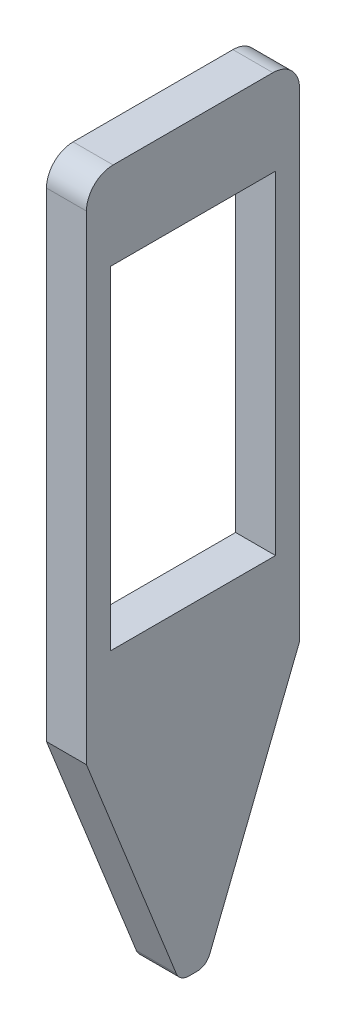
SolidWorks part; units mm, degrees
material "Teca"
ref_plane "Front Plane" through (0, 0, 0) normal (0, 0, 1) x (1, 0, 0)
ref_plane "Top Plane" through (0, 0, 0) normal (0, 1, 0) x (1, 0, 0)
ref_plane "Right Plane" through (0, 0, 0) normal (1, 0, 0) x (0, 0, -1)
sketch "Esboço1" plane through (0, 0, 0) normal (1, 0, 0) x (0, 0, -1)
  line L0 (0, -1015) -> (0, 48985) construction
  line L1 (-8, 19) -> (8, 19)
  line L2 (-8, 19) -> (-8, -19)
  line L4 (8, 19) -> (8, -19)
  line L5 (0, -15) -> (0, 19) construction
  line L6 (-8, 0) -> (8, 0) construction
  line L7 (-0.3216, -36.5938) -> (0.3216, -36.5938)
  line L8 (1.2508, -35.9635) -> (8, -19)
  line L9 (-8, -19) -> (-1.2508, -35.9635)
  line L11 (-6.2, 12.5) -> (6.2, 12.5)
  line L12 (-6.2, 12.5) -> (-6.2, -12.5)
  line L13 (-6.2, -12.5) -> (6.2, -12.5)
  line L14 (6.2, 12.5) -> (6.2, -12.5)
  line L15 (0, -12.5) -> (0, 12.5) construction
  line L16 (-6.2, 0) -> (6.2, 0) construction
  arc A0 (-0.3216, -36.5938) -> (-1.2508, -35.9635) centre (-0.3216, -35.5938) cw
  arc A1 (1.2508, -35.9635) -> (0.3216, -36.5938) centre (0.3216, -35.5938) cw
  point P0 (0, 0)
  point P9 (0, -36.5938)
  point P11 (-1, -36.5938)
  point P14 (1, -36.5938)
  point P15 (0, 0)
  dimension "D1" = 1
  dimension "D2" = 16
  dimension "D3" = 2
  dimension "D4" = 12.4
  dimension "D5" = 25
  dimension "D6" = 38
extrude "Ressalto-extrusão1" add sketch "Esboço1" along normal blind 3
fillet "Filete1" radius 2 2 edges at (1.5, 19, 8) (1.5, 19, -8)
